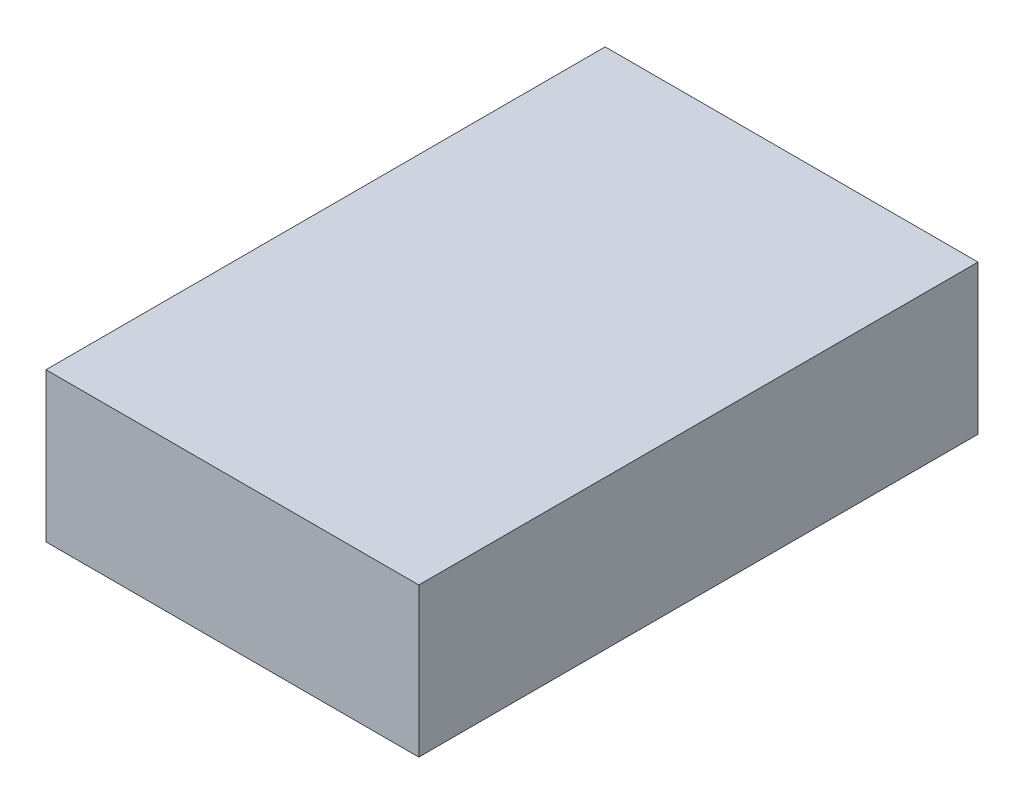
SolidWorks part; units mm, degrees
ref_plane "Front Plane" through (0, 0, 0) normal (0, 0, 1) x (1, 0, 0)
ref_plane "Top Plane" through (0, 0, 0) normal (0, 1, 0) x (1, 0, 0)
ref_plane "Right Plane" through (0, 0, 0) normal (1, 0, 0) x (0, 0, -1)
sketch "BaseS" plane through (0, 0, 0) normal (0, 1, 0) x (1, 0, 0)
  line L1 (-1, 1.5) -> (1, 1.5)
  line L2 (-1, 1.5) -> (-1, -1.5)
  line L3 (-1, -1.5) -> (1, -1.5)
  line L4 (1, 1.5) -> (1, -1.5)
  line L5 (-1, 1.5) -> (1, -1.5) construction
  line L6 (-1, -1.5) -> (1, 1.5) construction
  point P0 (0, 0)
  dimension "Width" = 2
  dimension "Length" = 3
extrude "Base" add sketch "BaseS" along normal blind 0.8
